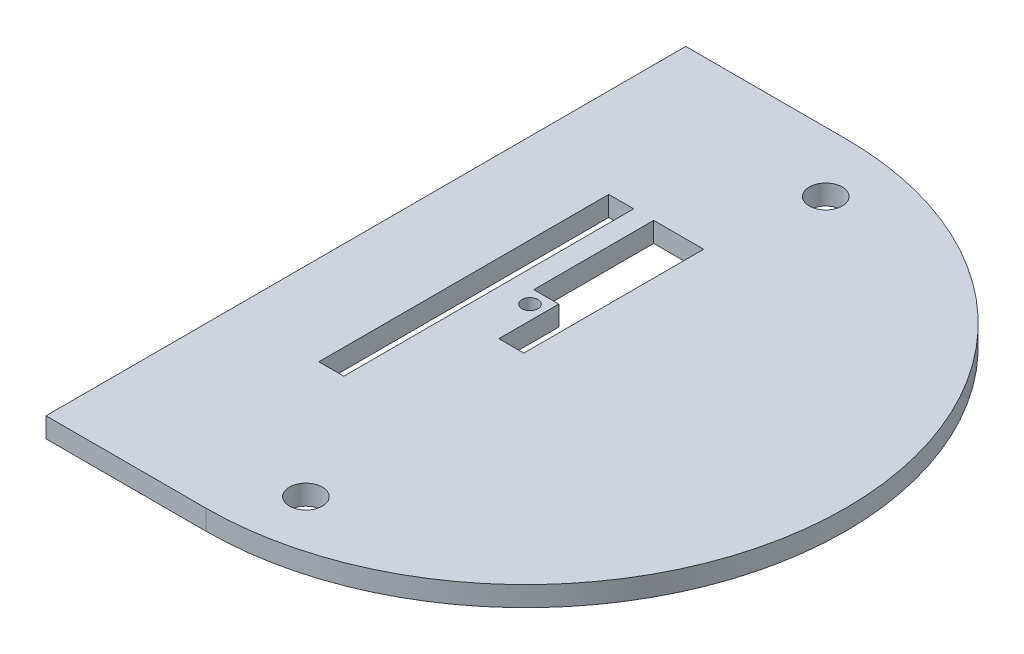
SolidWorks part; units mm, degrees
ref_plane "Alzado" through (0, 0, 0) normal (0, 0, 1) x (1, 0, 0)
ref_plane "Planta" through (0, 0, 0) normal (0, 1, 0) x (1, 0, 0)
ref_plane "Vista lateral" through (0, 0, 0) normal (1, 0, 0) x (0, 0, -1)
sketch "Croquis2" plane through (0, 0, 0) normal (0, 1, 0) x (1, 0, 0)
  line L0 (-71.2901, 11.7206) -> (-71.2901, -52.2794)
  line L1 (-71.2901, -52.2794) -> (-55.2901, -52.2794)
  line L2 (-71.2901, 11.7206) -> (-69.2901, 11.7206)
  line L3 (-55.2901, 11.7206) -> (-71.2901, 11.7206)
  line L4 (-62.3233, -4.9531) -> (-62.3233, -33.9531)
  line L5 (-62.3233, -4.9531) -> (-59.8233, -4.9531)
  line L6 (-62.3233, -33.9531) -> (-59.8233, -33.9531)
  line L7 (-59.8233, -33.9531) -> (-59.8233, -4.9531)
  line L8 (-59.8233, -4.9531) -> (-57.8233, -4.9531)
  line L9 (-57.8233, -4.9531) -> (-52.8233, -4.9531)
  line L10 (-57.8233, -4.9531) -> (-57.8233, -16.9531)
  line L11 (-57.8233, -16.9531) -> (-55.3233, -16.9531)
  line L12 (-55.3233, -16.9531) -> (-55.3233, -22.9531)
  line L13 (-55.3233, -22.9531) -> (-52.8233, -22.9531)
  line L14 (-52.8233, -22.9531) -> (-52.8233, -4.9531)
  arc A0 (-55.2901, -52.2794) -> (-55.2901, 11.7206) centre (-55.2901, -20.2794) ccw
  circle A1 centre (-56.7542, -18.3975) radius 0.8
extrude "Saliente-Extruir2" add sketch "Croquis2" along normal blind 2
hole_wizard "Taladro roscado M41" positions "Croquis6" profile "Croquis5" tap size "M4" standard "ISO"
sketch "Croquis6" plane through (0, 2, 0) normal (0, 1, 0) x (1, 0, 0)
  line L0 (-71.2901, -52.2794) -> (-55.2901, -52.2794) construction
  point P0 (-51.2901, 5.7206)
  point P2 (-51.2901, -46.2794)
  dimension "D1" = 6
  dimension "D2" = 4
  dimension "D3" = 4
  dimension "D4" = 6
sketch "Croquis5" plane through (-51.2901, 2, -5.7206) normal (1, 0, 0) x (0, 0, 1)
  line L0 (0, 0) -> (0, 12.4914)
  line L1 (0, 12.4914) -> (1.65, 11.5)
  line L2 (1.65, 11.5) -> (1.65, 0)
  line L5 (1.65, 0) -> (0, 0)
  line L10 (0, 12.4914) -> (-1.65, 11.5) construction
  line L11 (0, -6.35) -> (0, 107.95) construction
  dimension "Diámetro de perforador para roscar" = 3.3
  dimension "Profundidad de perforador para roscar" = 11.5
  dimension "Ángulo de perforador" = 118
cosmetic thread "Rosca de taladro1" parameters "D1"=2, "D2"=4
cosmetic thread "Rosca de taladro2" parameters "D1"=2, "D2"=4
